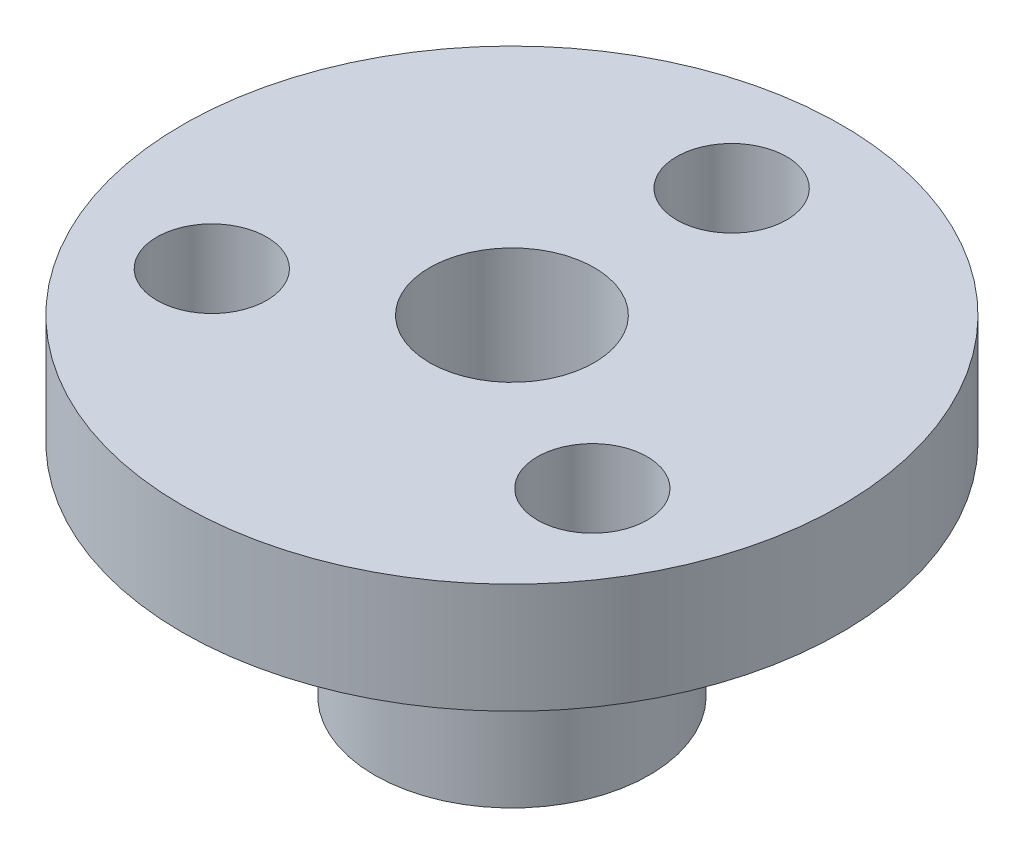
SolidWorks part; units mm, degrees
ref_plane "Front Plane" through (0, 0, 0) normal (0, 0, 1) x (1, 0, 0)
ref_plane "Top Plane" through (0, 0, 0) normal (0, 1, 0) x (1, 0, 0)
ref_plane "Right Plane" through (0, 0, 0) normal (1, 0, 0) x (0, 0, -1)
sketch "Sketch1" plane through (0, 0, 0) normal (0, 0, 1) x (1, 0, 0)
  line L0 (2.38, 9.53) -> (9.525, 9.53)
  line L1 (9.525, 9.53) -> (9.525, 6.35)
  line L2 (9.525, 6.35) -> (3.97, 6.35)
  line L3 (3.97, 6.35) -> (3.97, 0)
  line L4 (3.97, 0) -> (2.38, 0)
  line L6 (2.38, 0) -> (2.38, 9.53)
  line L7 (0, 10.3404) -> (0, 0) construction
  line L8 (0, 0) -> (2.38, 0) construction
  dimension "D1" = 3.18
  dimension "D2" = 9.53
  dimension "D3" = 2.38
  dimension "D4" = 9.525
  dimension "D5" = 3.97
revolve "Revolve1" add sketch "Sketch1" angle 360 about L7
sketch "Sketch2" plane through (0, 9.53, 0) normal (0, 1, 0) x (1, 0, 0)
  line L0 (0, 0) -> (0, 6.35) construction
  circle A0 centre (0, 6.35) radius 1.5875
  point P5 (0, 7.0843)
  dimension "D1" = 3.175
  dimension "D2" = 6.35
extrude "Cut-Extrude1" cut sketch "Sketch2" against normal through all
pattern_circular "CirPattern1" count 3 over 360 about axis through (0, 0, 0) along (0, 1, 0) of "Cut-Extrude1"
